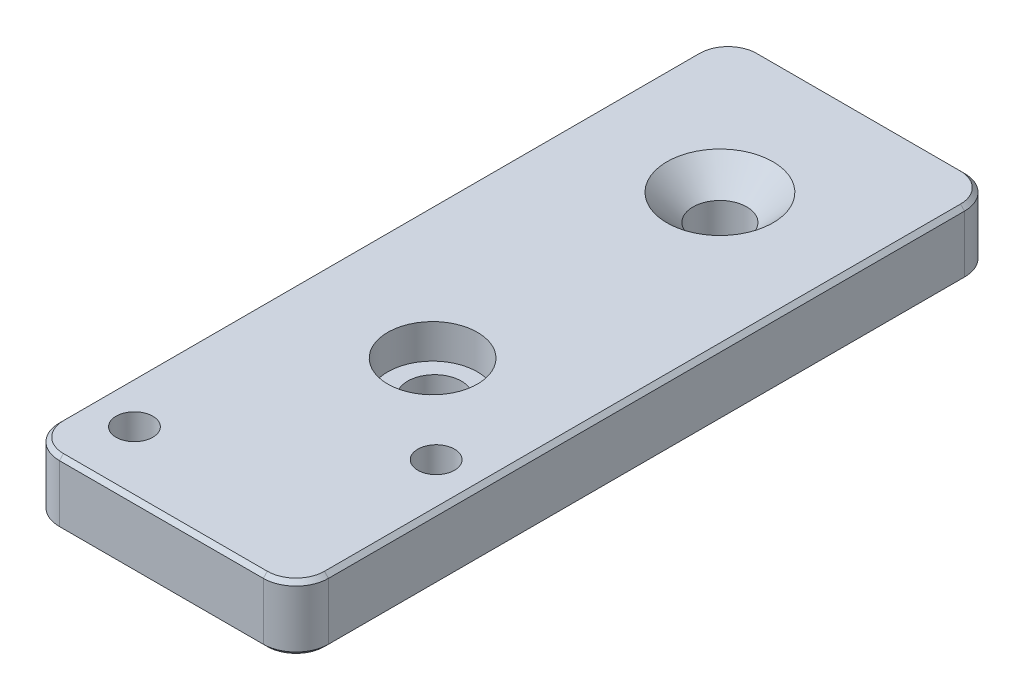
SolidWorks part; units mm, degrees
ref_plane "Front Plane" through (0, 0, 0) normal (0, 0, 1) x (1, 0, 0)
ref_plane "Top Plane" through (0, 0, 0) normal (0, 1, 0) x (1, 0, 0)
ref_plane "Right Plane" through (0, 0, 0) normal (1, 0, 0) x (0, 0, -1)
sketch "Sketch3" plane through (0, 0, 0) normal (0, 1, 0) x (1, 0, 0)
  line L1 (-16.5, -43) -> (16.5, -43)
  line L2 (-16.5, -43) -> (-16.5, 43)
  line L3 (-16.5, 43) -> (16.5, 43)
  line L4 (16.5, -43) -> (16.5, 43)
  line L5 (-16.5, -43) -> (16.5, 43) construction
  line L6 (-16.5, 43) -> (16.5, -43) construction
  circle A0 centre (0, 25.5) radius 3.3
  circle A1 centre (0, -9.5) radius 3.3
  circle A2 centre (11, -20.3) radius 2.25
  circle A3 centre (-11, -35.3) radius 2.25
  point P0 (0, 0)
  point P10 (0, 43)
  point P13 (0, 0)
  dimension "D3" = 6.6
  dimension "D4" = 6.6
  dimension "D7" = 4.5
  dimension "D1" = 33
  dimension "D2" = 86
  dimension "D5" = 17.5
  dimension "D6" = 35
  dimension "D8" = 7.7
  dimension "D9" = 15
  dimension "D10" = 5.5
  dimension "D11" = 22
extrude "Boss-Extrude2" add sketch "Sketch3" along normal blind 8
sketch "Sketch4" plane through (0, 8, 0) normal (0, 1, 0) x (1, 0, 0)
  circle A0 centre (0, -9.7363) radius 5.5
extrude "Cut-Extrude2" cut sketch "Sketch4" against normal blind 4.2
chamfer "Chamfer1" distance 3.2 angle 45 1 edges at (0, 8, -22.2)
sketch "Sketch5" plane through (0, 0, 0) normal (0, -1, 0) x (-1, 0, 0)
  circle A0 centre (11, -35.3) radius 4
  circle A1 centre (-11, -20.3) radius 4
  dimension "D1" = 8
  dimension "D2" = 8
extrude "Cut-Extrude3" cut sketch "Sketch5" against normal blind 4.4
fillet "Fillet1" radius 4 4 edges at (16.5, 4, 43) (-16.5, 4, 43) (-16.5, 4, -43) (16.5, 4, -43)
chamfer "Chamfer2" distance 0.5 angle 45 16 edges at (-15.3284, 8, -41.8284) (0, 8, -43) (15.3284, 8, -41.8284) (16.5, 8, 0) (15.3284, 8, 41.8284) (0, 8, 43) (-15.3284, 8, 41.8284) (-16.5, 8, 0) (-16.5, 0, 0) (-15.3284, 0, -41.8284) (0, 0, -43) (15.3284, 0, -41.8284) (16.5, 0, 0) (15.3284, 0, 41.8284) (-15.3284, 0, 41.8284) (0, 0, 43)
